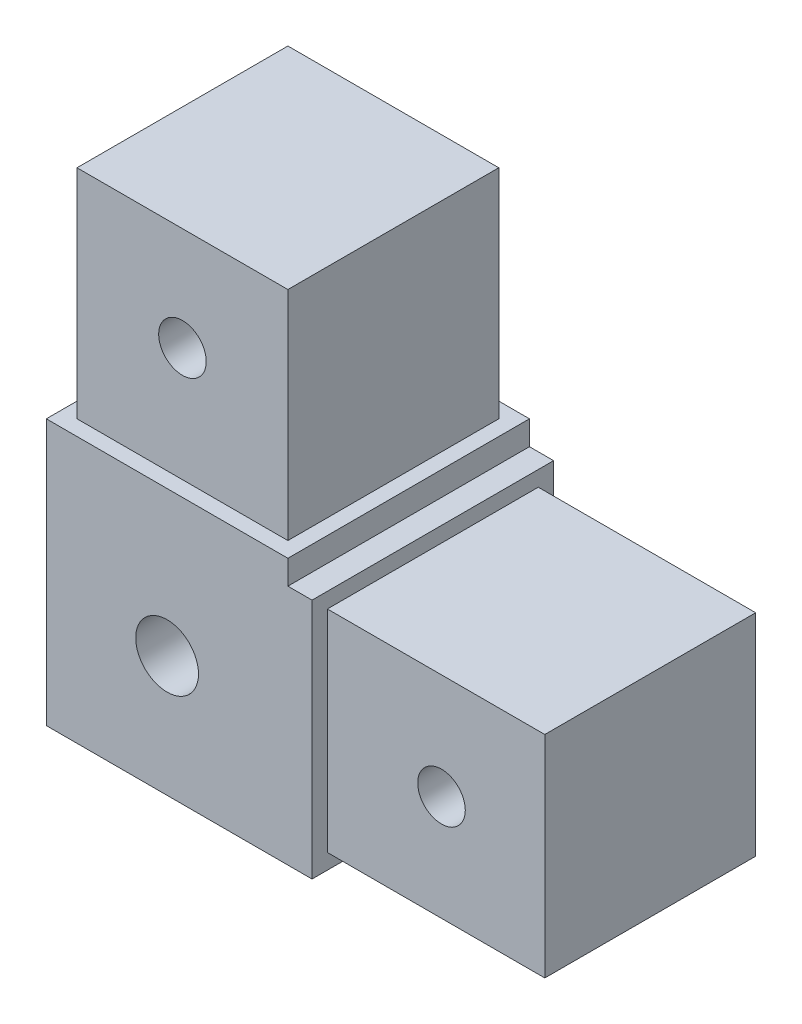
SolidWorks part; units mm, degrees
material "ALUMINUM 6061-T6"
ref_plane "Front Plane" through (0, 0, 0) normal (0, 0, 1) x (1, 0, 0)
ref_plane "Top Plane" through (0, 0, 0) normal (0, 1, 0) x (1, 0, 0)
ref_plane "Right Plane" through (0, 0, 0) normal (1, 0, 0) x (0, 0, -1)
sketch "Sketch1" plane through (0, 0, 0) normal (0, 0, 1) x (1, 0, 0)
  line L1 (-25.4, -25.4) -> (25.4, -25.4)
  line L2 (-25.4, -25.4) -> (-25.4, 25.4)
  line L3 (-25.4, 25.4) -> (25.4, 25.4)
  line L4 (25.4, -25.4) -> (25.4, 25.4)
  line L5 (-25.4, -25.4) -> (25.4, 25.4) construction
  line L6 (-25.4, 25.4) -> (25.4, -25.4) construction
  point P0 (0, 0)
  dimension "D1" = 50.8
  dimension "D2" = 50.8
extrude "Boss-Extrude1" add sketch "Sketch1" along normal mid plane 25.4
sketch "Sketch2" plane through (0, 0, 12.7) normal (0, 0, 1) x (1, 0, 0)
  line L1 (25.4, 25.4) -> (0, 25.4)
  line L2 (25.4, 25.4) -> (25.4, 0)
  line L3 (25.4, 0) -> (0, 0)
  line L4 (0, 25.4) -> (0, 0)
extrude "Cut-Extrude1" cut sketch "Sketch2" against normal through all
sketch "Sketch3" plane through (25.4, 0, 0) normal (1, 0, 0) x (0, 0, -1)
  line L0 (12.7, 0) -> (-12.7, 0) construction
  line L1 (-12.7, -25.4) -> (12.7, -25.4)
  line L2 (-12.7, -25.4) -> (-12.7, 0)
  line L3 (-12.7, 0) -> (12.7, 0)
  line L4 (12.7, -25.4) -> (12.7, 0)
  line L5 (-11.0871, -23.7871) -> (-11.0871, -1.6129)
  line L6 (-11.0871, -1.6129) -> (11.0871, -1.6129)
  line L7 (11.0871, -23.7871) -> (11.0871, -1.6129)
  line L8 (-11.0871, -23.7871) -> (11.0871, -23.7871)
  line L9 (12.7, -25.4) -> (12.7, 0) construction
  dimension "D1" = 1.6129
extrude "Cut-Extrude2" cut sketch "Sketch3" against normal blind 22.86
sketch "Sketch5" plane through (0, 25.4, 0) normal (0, 1, 0) x (1, 0, 0)
  line L0 (-1.6129, 11.0871) -> (-23.7871, 11.0871)
  line L1 (0, -12.7) -> (-25.4, -12.7)
  line L2 (0, -12.7) -> (0, 12.7)
  line L3 (0, 12.7) -> (-25.4, 12.7)
  line L4 (-25.4, -12.7) -> (-25.4, 12.7)
  line L5 (-23.7871, -11.0871) -> (-23.7871, 11.0871)
  line L6 (-1.6129, -11.0871) -> (-23.7871, -11.0871)
  line L7 (-1.6129, -11.0871) -> (-1.6129, 11.0871)
  dimension "D1" = 1.6129
extrude "Cut-Extrude4" cut sketch "Sketch5" against normal blind 22.86
sketch "Sketch7" plane through (0, 0, 12.7) normal (0, 0, 1) x (1, 0, 0)
  line L0 (-25.4, 2.54) -> (-25.4, -25.4) construction
  line L1 (-25.4, -25.4) -> (2.54, -25.4) construction
  circle A0 centre (-12.7, -12.7) radius 3.3
  dimension "D1" = 6.6
  dimension "D2" = 12.7
  dimension "D3" = 12.7
extrude "Cut-Extrude6" cut sketch "Sketch7" against normal through all
hole_wizard "Tap Drill for M6x1.0 Tap1" positions "Sketch9" profile "Sketch8" hole size "M6x1.0" standard "ANSI Metric" end condition through all
sketch "Sketch9" plane through (0, 0, 11.0871) normal (0, 0, 1) x (1, 0, 0)
  line L1 (2.54, -1.6129) -> (25.4, -1.6129) construction
  line L3 (2.54, 0) -> (2.54, -25.4) construction
  line L6 (-1.6129, 2.54) -> (-1.6129, 25.4) construction
  line L7 (-23.7871, 2.54) -> (-1.6129, 2.54) construction
  point P0 (14.54, -12.6979)
  point P2 (-12.6979, 14.54)
  dimension "D1" = 12
  dimension "D2" = 11.085
  dimension "D3" = 11.085
  dimension "D4" = 12
sketch "Sketch8" plane through (14.54, -12.6979, 11.0871) normal (1, 0, 0) x (0, -1, 0)
  line L0 (0, 0) -> (0, 23.7871)
  line L1 (0, 23.7871) -> (2.5, 23.7871)
  line L2 (2.5, 23.7871) -> (2.5, 0)
  line L5 (2.5, 0) -> (0, 0)
  line L11 (0, -6.35) -> (0, 107.95) construction
  dimension "Thru Hole Dia." = 5
  dimension "Thru Hole Depth" = 23.7871
